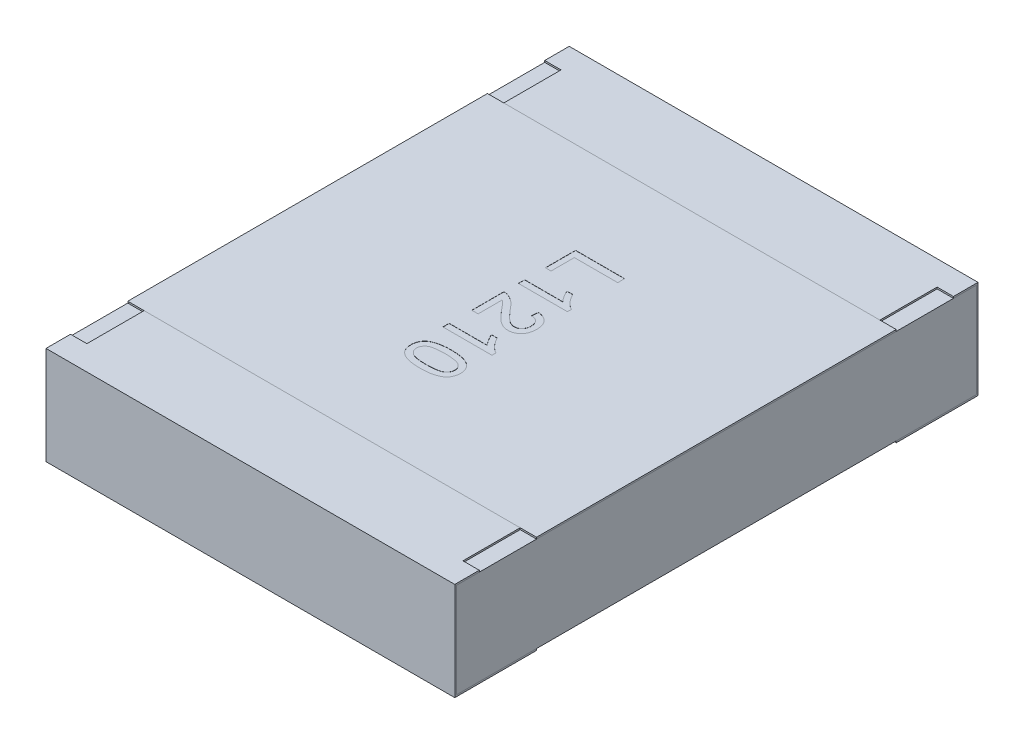
SolidWorks part; units mm, degrees
ref_plane "Front Plane" through (0, 0, 0) normal (0, 0, 1) x (1, 0, 0)
ref_plane "Top Plane" through (0, 0, 0) normal (0, 1, 0) x (1, 0, 0)
ref_plane "Right Plane" through (0, 0, 0) normal (1, 0, 0) x (0, 0, -1)
sketch "Sketch4" plane through (0, 0, 0) normal (1, 0, 0) x (0, 0, -1)
  line L0 (0, 0.1169) -> (0, -0.0721) construction
  line L1 (-1.6, 0) -> (0.3788, 0) construction
  line L2 (-1.6, 0.3) -> (-1.6, -0.3)
  line L3 (-1.6, -0.3) -> (-1.1, -0.3)
  line L4 (-1.1, 0.3) -> (-1.1, 0.29)
  line L5 (-1.1, 0.29) -> (-1.59, 0.29)
  line L6 (-1.59, 0.29) -> (-1.59, -0.29)
  line L7 (-1.59, -0.29) -> (-1.1, -0.29)
  line L8 (-1.1, -0.29) -> (-1.1, -0.3)
  line L9 (-1.1, 0.3) -> (-1.6, 0.3)
  line L10 (1.1, 0.3) -> (1.6, 0.3)
  line L11 (1.1, -0.29) -> (1.1, -0.3)
  line L12 (1.59, -0.29) -> (1.1, -0.29)
  line L13 (1.59, 0.29) -> (1.59, -0.29)
  line L14 (1.1, 0.29) -> (1.59, 0.29)
  line L15 (1.1, 0.3) -> (1.1, 0.29)
  line L16 (1.6, -0.3) -> (1.1, -0.3)
  line L17 (1.6, 0.3) -> (1.6, -0.3)
  dimension "LENGTH" = 1.6
  dimension "HEIGHT" = 0.6
  dimension "END CAP TOP LENGTH" = 0.5
  dimension "END CAP BOTTOM LENGTH" = 0.5
  dimension "D5" = 0.01
  dimension "D6" = 0.01
extrude "Boss-Extrude2" add sketch "Sketch4" along normal mid plane 2.5
sketch "Sketch5" plane through (0, 0, 0) normal (1, 0, 0) x (0, 0, -1)
  line L1 (-1.59, 0.29) -> (1.59, 0.29)
  line L2 (-1.59, 0.29) -> (-1.59, -0.29)
  line L3 (-1.59, -0.29) -> (1.59, -0.29)
  line L4 (1.59, 0.29) -> (1.59, -0.29)
extrude "Boss-Extrude3" add sketch "Sketch5" along normal up to surface and the other way up to surface separate body
sketch "Sketch6" plane through (0, 0.3, 0) normal (0, 1, 0) x (1, 0, 0)
  line L0 (-1.25, 1.6) -> (-1.25, 1.1) construction
  line L1 (-1.25, 1.45) -> (-1.15, 1.45)
  line L2 (-1.25, 1.45) -> (-1.25, 1.1)
  line L3 (-1.25, 1.1) -> (-1.15, 1.1)
  line L4 (-1.15, 1.45) -> (-1.15, 1.1)
  line L5 (1.25, 1.1) -> (-1.25, 1.1) construction
  line L6 (0, 0.0345) -> (0, -0.0345) construction
  line L7 (-0.0325, 0) -> (0.03, 0) construction
  line L8 (1.25, 1.45) -> (1.25, 1.1)
  line L9 (1.25, 1.1) -> (1.15, 1.1)
  line L10 (1.15, 1.45) -> (1.15, 1.1)
  line L11 (1.25, 1.45) -> (1.15, 1.45)
  line L12 (1.25, -1.45) -> (1.15, -1.45)
  line L13 (1.25, -1.45) -> (1.25, -1.1)
  line L14 (1.25, -1.1) -> (1.15, -1.1)
  line L15 (1.15, -1.45) -> (1.15, -1.1)
  line L16 (-1.25, -1.45) -> (-1.15, -1.45)
  line L17 (-1.25, -1.45) -> (-1.25, -1.1)
  line L18 (-1.25, -1.1) -> (-1.15, -1.1)
  line L19 (-1.15, -1.45) -> (-1.15, -1.1)
  dimension "TOP CUT WIDTH" = 0.1
  dimension "TOP CUT LENGTH" = 0.35
extrude "Cut-Extrude1" cut sketch "Sketch6" against normal up to surface (0.01 mm away) up to face at (0, 0.29, 0)
sketch "Sketch7" plane through (0, 0.29, 0) normal (0, 1, 0) x (1, 0, 0)
  line L1 (-1.25, 1.1) -> (1.25, 1.1)
  line L2 (-1.25, 1.1) -> (-1.25, -1.1)
  line L3 (-1.25, -1.1) -> (1.25, -1.1)
  line L4 (1.25, 1.1) -> (1.25, -1.1)
  line L5 (1.15, -1.1) -> (-1.15, -1.1) construction
  line L6 (1.15, 1.1) -> (-1.15, 1.1) construction
  line L7 (-1.25, -1.59) -> (-1.25, 1.59) construction
  line L8 (1.25, 1.59) -> (1.25, -1.59) construction
extrude "Boss-Extrude4" add sketch "Sketch7" along normal up to surface (0.01 mm away) separate body up to face at (0, 0.3, -1.4)
sketch "Sketch13" plane through (0, 0.3, 0) normal (0, 1, 0) x (1, 0, 0)
  line L0 (-0.15, 0.5735) -> (-0.15, -0.5735) construction
  line L1 (0, 0) -> (-0.15, 0) construction
  text T0 "L1210" font "Arial" height 0.3
  dimension "D1" = 0.15
extrude "TEXT1210" cut sketch "Sketch13" against normal blind 0.001
